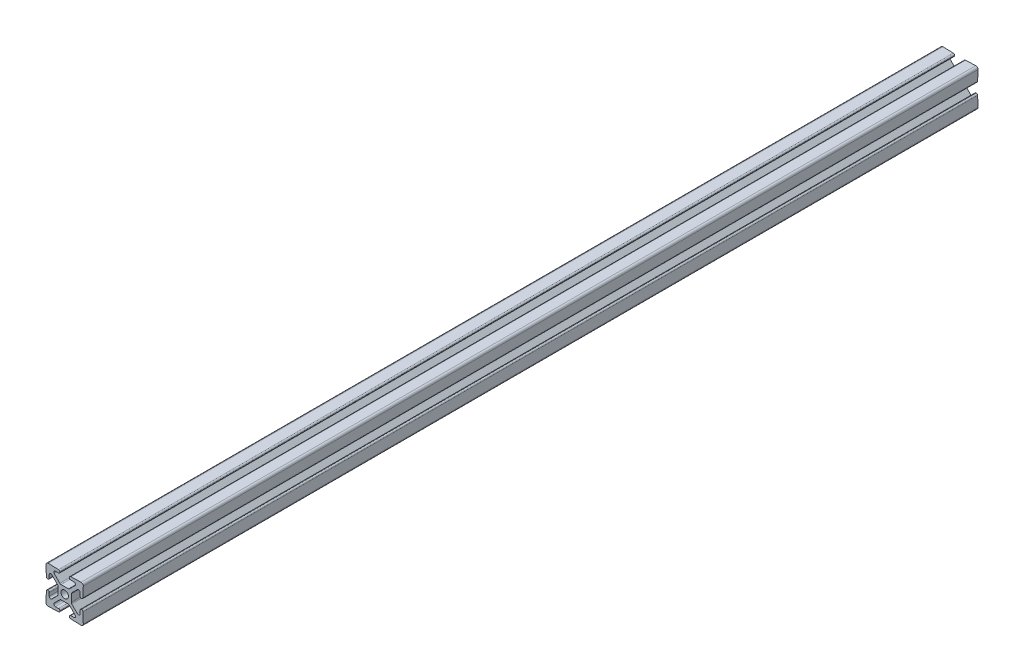
SolidWorks part; units mm, degrees
material "6061 Alloy"
ref_plane "Front Plane" through (0, 0, 0) normal (0, 0, 1) x (1, 0, 0)
ref_plane "Top Plane" through (0, 0, 0) normal (0, 1, 0) x (1, 0, 0)
ref_plane "Right Plane" through (0, 0, 0) normal (1, 0, 0) x (0, 0, -1)
sketch "Sketch1" plane through (0, 0, 0) normal (0, 0, 1) x (1, 0, 0)
  line L1 (3.2385, -11.4554) -> (3.2385, -11.4907)
  line L2 (-7.1065, 8.6691) -> (-3.2584, 4.821)
  line L3 (-3.2385, 11.4907) -> (-3.2385, 11.4554)
  line L6 (-4.2037, 10.4902) -> (-6.3521, 10.4902)
  line L7 (-11.176, 12.7) -> (-4.17, 12.4553)
  line L8 (11.4554, 3.2385) -> (11.4907, 3.2385)
  line L9 (11.4554, -3.2385) -> (11.4907, -3.2385)
  line L11 (-4.821, 3.2584) -> (-8.6691, 7.1065)
  line L12 (-10.4902, 6.3521) -> (-10.4902, 4.2037)
  line L13 (-12.7, 11.176) -> (-12.4553, 4.17)
  line L15 (-4.5085, -2.504) -> (-4.5085, 2.504)
  line L16 (6.3521, -10.4902) -> (4.2037, -10.4902)
  line L22 (-2.504, 4.5085) -> (2.504, 4.5085)
  line L23 (-3.2584, -4.821) -> (-7.1065, -8.6691)
  line L24 (-11.176, -12.7) -> (-4.17, -12.4553)
  line L25 (-12.7, -11.176) -> (-12.4553, -4.17)
  line L26 (-10.4902, -4.2037) -> (-10.4902, -6.3521)
  line L27 (-8.6691, -7.1065) -> (-4.821, -3.2584)
  line L36 (8.6691, -7.1065) -> (4.821, -3.2584)
  line L38 (10.4902, -4.2037) -> (10.4902, -6.3521)
  line L39 (12.7, -11.176) -> (12.4553, -4.17)
  line L42 (11.176, -12.7) -> (4.17, -12.4553)
  line L43 (3.2584, -4.821) -> (7.1065, -8.6691)
  line L47 (4.5085, -2.504) -> (4.5085, 2.504)
  line L48 (12.7, 11.176) -> (12.4553, 4.17)
  line L49 (10.4902, 6.3521) -> (10.4902, 4.2037)
  line L50 (4.821, 3.2584) -> (8.6691, 7.1065)
  line L52 (2.504, -4.5085) -> (-2.504, -4.5085)
  line L56 (11.176, 12.7) -> (4.17, 12.4553)
  line L57 (4.2037, 10.4902) -> (6.3521, 10.4902)
  line L59 (-6.3521, -10.4902) -> (-4.2037, -10.4902)
  line L60 (3.2385, 11.4907) -> (3.2385, 11.4554)
  line L61 (7.1065, 8.6691) -> (3.2584, 4.821)
  line L66 (-11.4554, -3.2385) -> (-11.4907, -3.2385)
  line L68 (-11.4554, 3.2385) -> (-11.4907, 3.2385)
  line L74 (-3.2385, -11.4554) -> (-3.2385, -11.4907)
  arc A1 (-3.2385, 11.4907) -> (-4.17, 12.4553) centre (-4.2037, 11.4907) ccw
  arc A4 (-4.2037, 10.4902) -> (-3.2385, 11.4554) centre (-4.2037, 11.4554) ccw
  arc A6 (-6.3521, 10.4902) -> (-7.1065, 8.6691) centre (-6.3521, 9.4234) ccw
  arc A8 (-12.4553, 4.17) -> (-11.4907, 3.2385) centre (-11.4907, 4.2037) ccw
  arc A9 (-11.176, 12.7) -> (-12.7, 11.176) centre (-11.176, 11.176) ccw
  arc A12 (-8.6691, 7.1065) -> (-10.4902, 6.3521) centre (-9.4234, 6.3521) ccw
  arc A13 (-11.4554, 3.2385) -> (-10.4902, 4.2037) centre (-11.4554, 4.2037) ccw
  arc A16 (-4.821, -3.2584) -> (-4.5085, -2.504) centre (-5.5753, -2.504) ccw
  arc A17 (-4.5085, 2.504) -> (-4.821, 3.2584) centre (-5.5753, 2.504) ccw
  arc A22 (3.2584, 4.821) -> (2.504, 4.5085) centre (2.504, 5.5753) cw
  arc A23 (10.4902, -6.3521) -> (8.6691, -7.1065) centre (9.4234, -6.3521) cw
  arc A24 (10.4902, -4.2037) -> (11.4554, -3.2385) centre (11.4554, -4.2037) cw
  arc A25 (11.4907, -3.2385) -> (12.4553, -4.17) centre (11.4907, -4.2037) cw
  arc A26 (12.7, -11.176) -> (11.176, -12.7) centre (11.176, -11.176) cw
  arc A28 (-2.504, -4.5085) -> (-3.2584, -4.821) centre (-2.504, -5.5753) ccw
  arc A29 (-4.17, -12.4553) -> (-3.2385, -11.4907) centre (-4.2037, -11.4907) ccw
  arc A30 (-3.2385, -11.4554) -> (-4.2037, -10.4902) centre (-4.2037, -11.4554) ccw
  arc A31 (-7.1065, -8.6691) -> (-6.3521, -10.4902) centre (-6.3521, -9.4234) ccw
  arc A32 (-12.7, -11.176) -> (-11.176, -12.7) centre (-11.176, -11.176) ccw
  arc A33 (-11.4907, -3.2385) -> (-12.4553, -4.17) centre (-11.4907, -4.2037) ccw
  arc A34 (-10.4902, -4.2037) -> (-11.4554, -3.2385) centre (-11.4554, -4.2037) ccw
  arc A35 (-10.4902, -6.3521) -> (-8.6691, -7.1065) centre (-9.4234, -6.3521) ccw
  arc A36 (7.1065, -8.6691) -> (6.3521, -10.4902) centre (6.3521, -9.4234) cw
  arc A37 (3.2385, -11.4554) -> (4.2037, -10.4902) centre (4.2037, -11.4554) cw
  arc A38 (-3.2584, 4.821) -> (-2.504, 4.5085) centre (-2.504, 5.5753) ccw
  arc A39 (4.17, -12.4553) -> (3.2385, -11.4907) centre (4.2037, -11.4907) cw
  arc A40 (2.504, -4.5085) -> (3.2584, -4.821) centre (2.504, -5.5753) cw
  circle A44 centre (0, 0) radius 2.5527
  arc A45 (4.5085, 2.504) -> (4.821, 3.2584) centre (5.5753, 2.504) cw
  arc A46 (4.821, -3.2584) -> (4.5085, -2.504) centre (5.5753, -2.504) cw
  arc A47 (11.4554, 3.2385) -> (10.4902, 4.2037) centre (11.4554, 4.2037) cw
  arc A48 (8.6691, 7.1065) -> (10.4902, 6.3521) centre (9.4234, 6.3521) cw
  arc A49 (11.176, 12.7) -> (12.7, 11.176) centre (11.176, 11.176) cw
  arc A53 (12.4553, 4.17) -> (11.4907, 3.2385) centre (11.4907, 4.2037) cw
  arc A54 (6.3521, 10.4902) -> (7.1065, 8.6691) centre (6.3521, 9.4234) cw
  arc A56 (4.2037, 10.4902) -> (3.2385, 11.4554) centre (4.2037, 11.4554) cw
  arc A58 (3.2385, 11.4907) -> (4.17, 12.4553) centre (4.2037, 11.4907) cw
  dimension "D5" = 5.1054
  dimension "D1" = 12.7
  dimension "D2" = 25.4
  dimension "D3" = 25.4
  dimension "D4" = 12.7
extrude "Extrude1" add sketch "Sketch1" along normal mid plane 609.6
